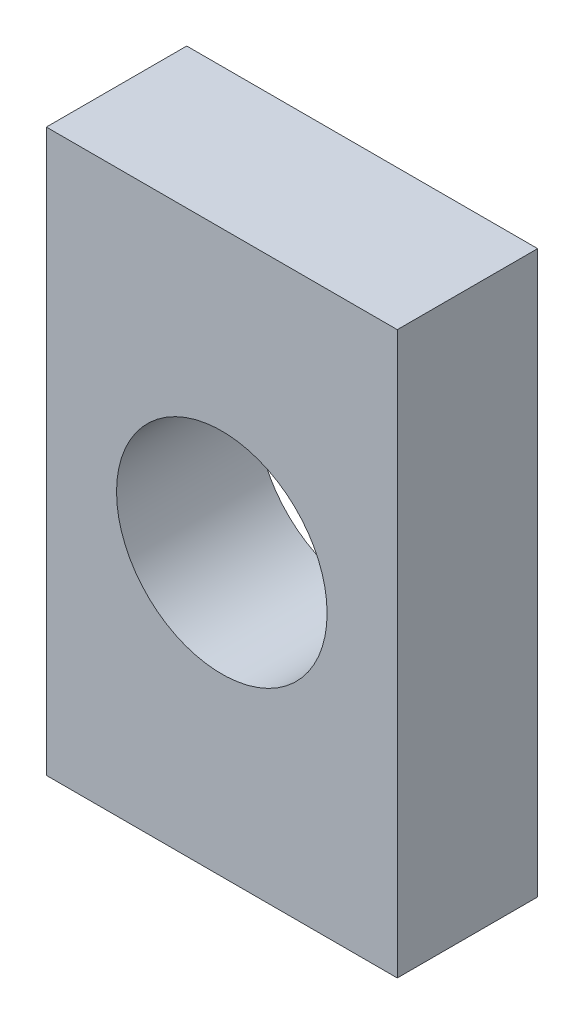
SolidWorks part; units mm, degrees
ref_plane "Plano frontal" through (0, 0, 0) normal (0, 0, 1) x (1, 0, 0)
ref_plane "Plano superior" through (0, 0, 0) normal (0, 1, 0) x (1, 0, 0)
ref_plane "Plano direito" through (0, 0, 0) normal (1, 0, 0) x (0, 0, -1)
sketch "Esboço1" plane through (0, 0, 0) normal (0, 0, 1) x (1, 0, 0)
  line L1 (-2.5, 4) -> (2.5, 4)
  line L2 (-2.5, 4) -> (-2.5, -4)
  line L3 (-2.5, -4) -> (2.5, -4)
  line L4 (2.5, 4) -> (2.5, -4)
  line L5 (-2.5, 4) -> (2.5, -4) construction
  line L6 (-2.5, -4) -> (2.5, 4) construction
  circle A0 centre (0, 0) radius 1.5
  dimension "D2" = 3
  dimension "D1" = 8
  dimension "D3" = 5
extrude "Ressalto-extrusão1" add sketch "Esboço1" along normal blind 2
